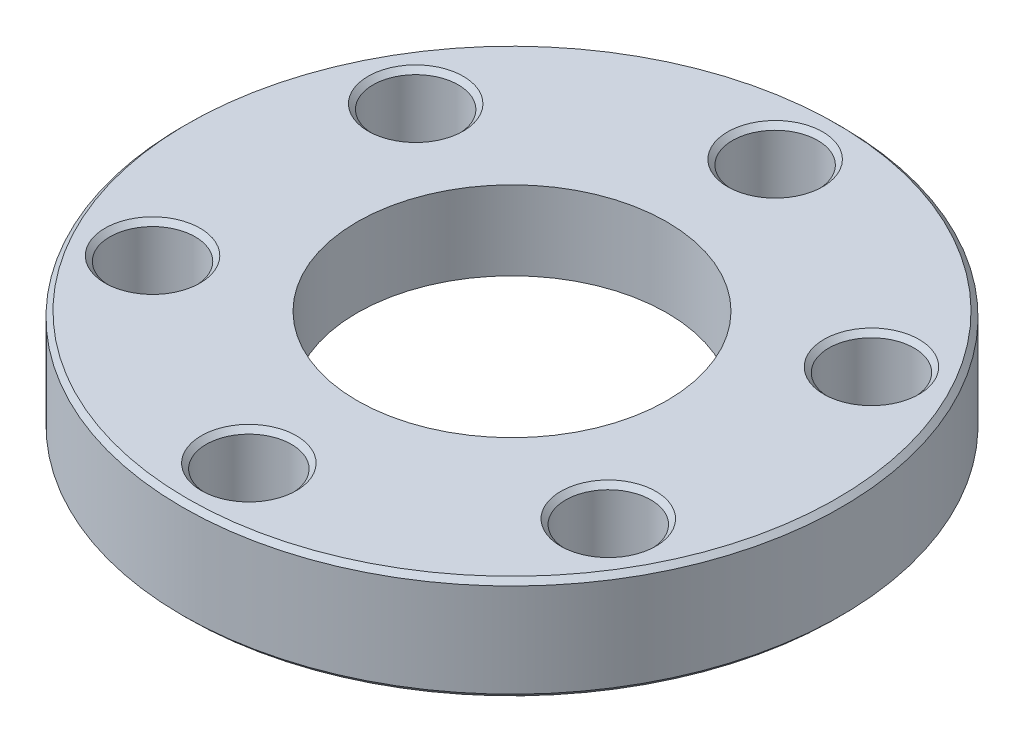
SolidWorks part; units mm, degrees
ref_plane "Front Plane" through (0, 0, 0) normal (0, 0, 1) x (1, 0, 0)
ref_plane "Top Plane" through (0, 0, 0) normal (0, 1, 0) x (1, 0, 0)
ref_plane "Right Plane" through (0, 0, 0) normal (1, 0, 0) x (0, 0, -1)
sketch "Sketch1" plane through (0, 0, 0) normal (0, 1, 0) x (1, 0, 0)
  circle A0 centre (0, 0) radius 16.891
  circle A1 centre (0, 0) radius 7.9375
  dimension "D1" = 33.782
  dimension "D2" = 15.875
extrude "Boss-Extrude1" add sketch "Sketch1" along normal blind 12.7
sketch "Sketch2" plane through (0, 12.7, 0) normal (0, 1, 0) x (1, 0, 0)
  circle A0 centre (0, 0) radius 20.6375
  dimension "D1" = 41.275
extrude "Cut-Extrude1" cut sketch "Sketch2" against normal blind 7.3914
chamfer "Chamfer1" distance 0.254 angle 45 2 edges at (0, 0, 16.891) (0, 5.3086, 16.891)
sketch "Sketch3" plane through (0, 0, 0) normal (0, 0, 1) x (1, 0, 0)
  line L0 (-10.7188, 0) -> (-10.7188, 1.2446)
  line L1 (-10.7188, 1.2446) -> (-9.144, 0.6604)
  line L2 (-9.144, 0.6604) -> (-9.144, 1.27)
  line L3 (-9.144, 1.27) -> (0, 1.27)
  line L4 (-10.7188, 0) -> (0, 0)
  line L5 (0, 0) -> (0, 1.27)
  dimension "D1" = 10.7188
  dimension "D2" = 9.144
  dimension "D3" = 1.2446
  dimension "D4" = 0.6096
  dimension "D5" = 1.27
revolve "Cut-Revolve1" cut sketch "Sketch3" angle 360 about axis through (0, 12.7, 0) along (0, -1, 0)
sketch "Sketch4" plane through (0, 5.3086, 0) normal (0, 1, 0) x (1, 0, 0)
  circle A0 centre (0, 13.4874) radius 2.1844
  dimension "D1" = 4.3688
  dimension "D2" = 13.4874
extrude "Cut-Extrude2" cut sketch "Sketch4" against normal through all
chamfer "Chamfer2" distance 0.254 angle 45 2 edges at (0, 0, -11.303) (0, 5.3086, -11.303)
pattern_circular "CirPattern1" count 6 every 60 about axis through (0, 0, 0) along (0, 1, 0) of "Cut-Extrude2", "Chamfer2"
